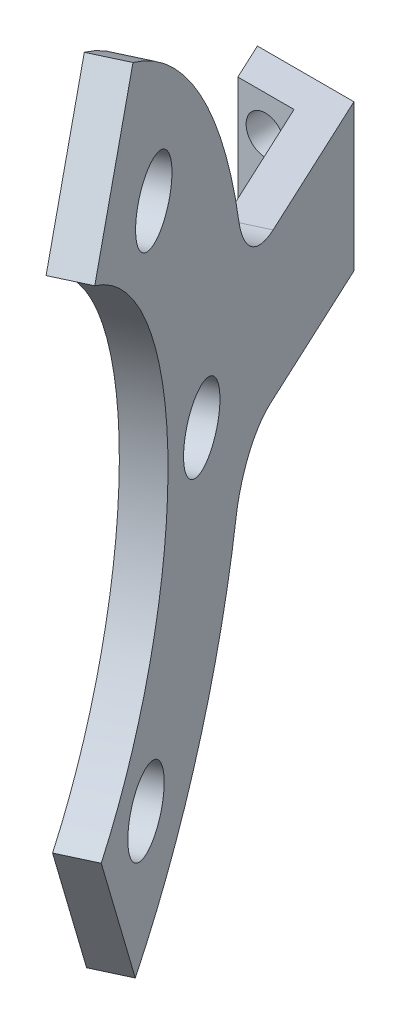
SolidWorks part; units mm, degrees
material "201 Annealed Stainless Steel (SS)"
ref_plane "Front Plane" through (0, 0, 0) normal (0, 0, 1) x (1, 0, 0)
ref_plane "Top Plane" through (0, 0, 0) normal (0, 1, 0) x (1, 0, 0)
ref_plane "Right Plane" through (0, 0, 0) normal (1, 0, 0) x (0, 0, -1)
sketch "Sketch1" plane through (0, 0, 0) normal (0, 1, 0) x (1, 0, 0)
  line L3 (34.5181, -15.55) -> (32.7602, -16.5037)
  line L7 (25.997, -2) -> (32.7602, -16.5037)
  line L8 (27.267, 0) -> (34.5181, -15.55)
  line L11 (22.9296, -2) -> (25.997, -2)
  line L12 (27.267, 0) -> (21.997, 0)
  line L13 (21.997, 0) -> (22.9296, -2)
  dimension "D2" = 2
extrude "Boss-Extrude1" add sketch "Sketch1" along normal blind 8
sketch "Sketch5" plane through (22.397, 0, -10.4439) normal (0.9063, 0, -0.4226) x (-0.4226, 0, -0.9063)
  line L0 (-40.7809, 18.7361) -> (-36.4672, 26.4289)
  line L1 (-40.0493, -9.0573) -> (-36.2057, -17.037)
  line L2 (-32.5193, 4.1187) -> (-28.7015, 4) construction
  arc A0 (-36.2057, -17.037) -> (-36.4672, 26.4289) centre (-48.6919, 4.6216) ccw
  arc A1 (-38.3829, -12.5169) -> (-38.9127, 22.0677) centre (-48.6919, 4.6216) ccw construction
  arc A2 (-40.0493, -9.0573) -> (-40.7809, 18.7361) centre (-48.6919, 4.6216) ccw
  dimension "D5" = 25
  dimension "D1" = 125
  dimension "D2" = 62.5
extrude "Boss-Extrude2" add sketch "Sketch5" against normal blind 2 contours L1 A0 L0 A2
sketch "Sketch3" plane through (20.5877, 0, -9.6002) normal (-0.9063, 0, 0.4226) x (0.4226, 0, 0.9063)
  circle A0 centre (28.7015, 4) radius 2.05
  circle A1 centre (48.6919, 4.6216) radius 20 construction
  circle A2 centre (34.117, 18.3174) radius 2.05
  circle A3 centre (48.0703, 24.6119) radius 2.05
  circle A4 centre (62.3876, 19.1964) radius 2.05
  circle A5 centre (68.6822, 5.2431) radius 2.05
  circle A6 centre (63.2667, -9.0742) radius 2.05
  circle A7 centre (49.3134, -15.3688) radius 2.05
  circle A8 centre (34.9961, -9.9533) radius 2.05
  point P23 (48.6919, 4.6216)
  dimension "D1" = 4.1
  dimension "D3" = 8
extrude "Cut-Extrude3" cut sketch "Sketch3" against normal blind 10 and the other way blind 10
fillet "Fillet2" radius 4 2 edges at (31.687, 0, 11.8406) (31.6019, 8, 11.6579)
sketch "Sketch6" plane through (0, 0, 2) normal (0, 0, 1) x (1, 0, 0)
  line L0 (22.9296, 0) -> (25.997, 0) construction
  line L1 (22.9296, 8) -> (25.997, 8) construction
  line L2 (22.9296, 8) -> (22.9296, 0) construction
  circle A0 centre (24.4296, 6) radius 1.05
  circle A1 centre (24.4296, 2) radius 1.05
  dimension "D1" = 2.1
  dimension "D2" = 2.1
  dimension "D3" = 2
  dimension "D4" = 2
  dimension "D5" = 1.5
  dimension "D6" = 1.5
extrude "Cut-Extrude4" cut sketch "Sketch6" against normal through all
equation "\"D2@Sketch5\"=\"D1@Sketch5\"/2"
